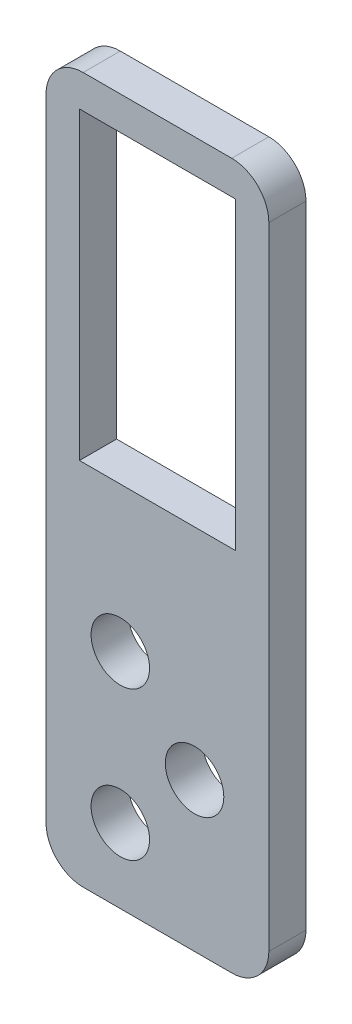
SolidWorks part; units mm, degrees
material "6061-T6 (SS)"
ref_plane "Front Plane" through (0, 0, 0) normal (0, 0, 1) x (1, 0, 0)
ref_plane "Top Plane" through (0, 0, 0) normal (0, 1, 0) x (1, 0, 0)
ref_plane "Right Plane" through (0, 0, 0) normal (1, 0, 0) x (0, 0, -1)
sketch "Sketch1" plane through (0, 0, 0) normal (0, 0, 1) x (1, 0, 0)
  line L0 (0, 0) -> (0, -63.5)
  line L5 (0, -63.5) -> (38.1, -63.5)
  line L6 (38.1, 0) -> (38.1, -63.5)
  line L7 (0, 0) -> (38.1, 0)
  line L8 (12.7, -63.5) -> (12.7, -120.6713)
  line L9 (0, -63.5) -> (0, -120.6713)
  line L10 (38.1, -63.5) -> (38.1, -120.6713)
  line L11 (25.4, -63.5) -> (25.4, -120.6713)
  line L12 (0, -120.6713) -> (38.1, -120.6713)
  line L13 (0, -31.75) -> (38.1, -31.75) construction
  line L14 (19.05, 0) -> (19.05, -63.5) construction
  line L16 (32.385, -57.785) -> (5.715, -57.785)
  line L17 (32.385, -57.785) -> (32.385, -5.715)
  line L18 (32.385, -5.715) -> (5.715, -5.715)
  line L19 (5.715, -57.785) -> (5.715, -5.715)
  line L20 (32.385, -57.785) -> (5.715, -5.715) construction
  line L21 (32.385, -5.715) -> (5.715, -57.785) construction
  circle A0 centre (25.4, -95.2713) radius 5
  circle A1 centre (12.7, -107.9713) radius 5
  circle A2 centre (12.7, -82.5713) radius 5
  point P0 (19.05, -31.75)
  dimension "D13" = 10
  dimension "D1" = 38.1
  dimension "D2" = 63.5
  dimension "D3" = 26.67
  dimension "D4" = 52.07
  dimension "D7" = 12.7
  dimension "D8" = 12.7
  dimension "D9" = 19.0713
  dimension "D10" = 12.7
  dimension "D11" = 12.7
  dimension "D12" = 12.7
extrude "Boss-Extrude1" add sketch "Sketch1" along normal blind 6.35
fillet "Fillet1" radius 6.35 4 edges at (38.1, 0, 3.175) (0, 0, 3.175) (0, -120.6713, 3.175) (38.1, -120.6713, 3.175)
